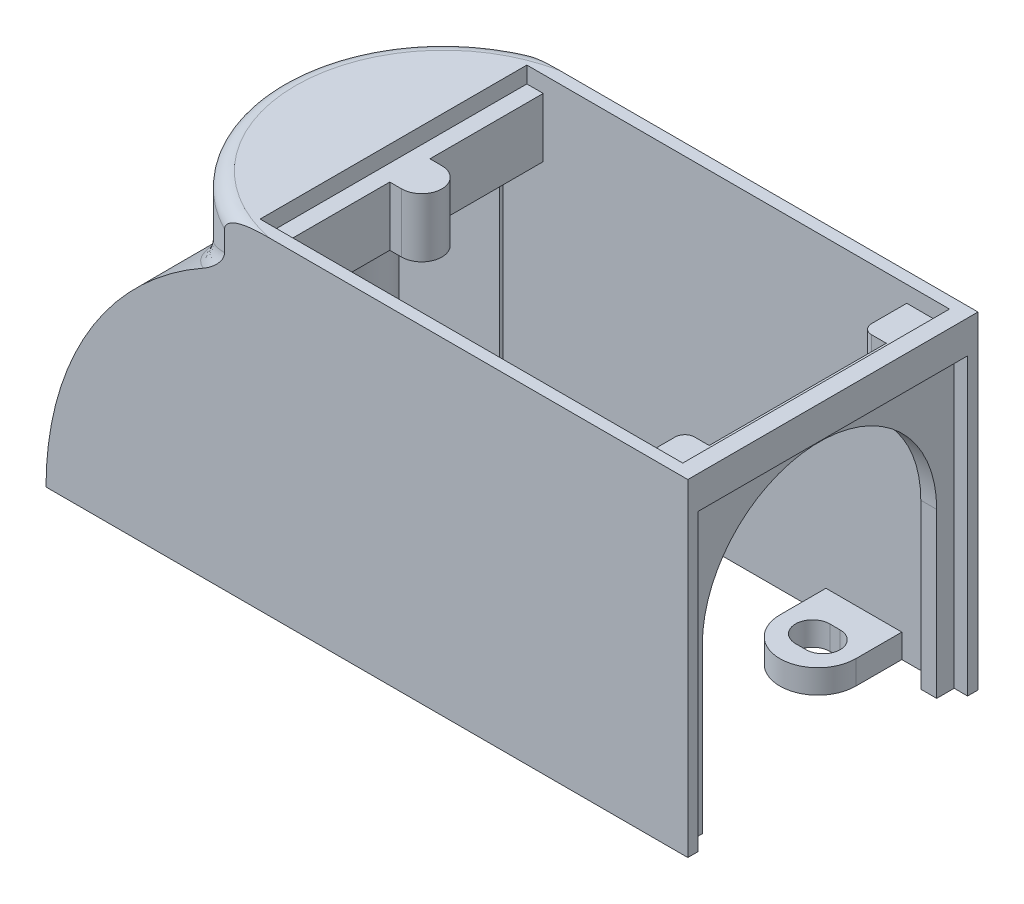
SolidWorks part; units mm, degrees
material "ABS"
ref_plane "Front Plane" through (0, 0, 0) normal (0, 0, 1) x (1, 0, 0)
ref_plane "Top Plane" through (0, 0, 0) normal (0, 1, 0) x (1, 0, 0)
ref_plane "Right Plane" through (0, 0, 0) normal (1, 0, 0) x (0, 0, -1)
sketch "Sketch1" plane through (0, 0, 0) normal (0, 1, 0) x (1, 0, 0)
  line L1 (0, 0) -> (75, 0)
  line L2 (0, 0) -> (0, 49.53)
  line L3 (0, 49.53) -> (75, 49.53)
  line L4 (75, 0) -> (75, 49.53)
  dimension "D1" = 49.53
  dimension "D2" = 75
extrude "Boss-Extrude1" add sketch "Sketch1" along normal blind 55.88
sketch "Sketch2" plane through (0, 55.88, 0) normal (0, 1, 0) x (1, 0, 0)
  line L0 (0, 0) -> (75, 0) construction
  line L1 (75, 49.53) -> (72, 49.53)
  line L2 (75, 49.53) -> (75, 0)
  line L3 (75, 0) -> (72, 0)
  line L4 (72, 49.53) -> (72, 0)
  line L5 (0, 49.53) -> (0, 0) construction
  line L6 (75, 49.53) -> (0, 49.53)
  line L7 (75, 49.53) -> (75, 47.53)
  line L8 (75, 47.53) -> (0, 47.53)
  line L9 (0, 49.53) -> (0, 47.53)
  line L10 (66.491, 41.529) -> (66.491, 49.53)
  line L11 (0, 49.53) -> (2.794, 49.53)
  line L12 (0, 49.53) -> (0, 0)
  line L13 (0, 0) -> (2.794, 0)
  line L14 (2.794, 49.53) -> (2.794, 0)
  line L15 (0, 0) -> (75, 0)
  line L16 (0, 0) -> (0, 2)
  line L17 (0, 2) -> (75, 2)
  line L18 (75, 0) -> (75, 2)
  line L19 (64.84, 41.529) -> (64.84, 47.53)
  line L20 (66.491, 39.878) -> (72, 39.878)
  line L21 (66.491, 0) -> (66.491, 8.001)
  line L22 (75, 8.001) -> (66.491, 8.001)
  line L23 (66.491, 9.652) -> (72, 9.652)
  line L24 (64.84, 8.001) -> (64.84, 2)
  line L25 (75, 24.765) -> (69, 24.765)
  line L26 (2.794, 24.765) -> (4.826, 24.765)
  line L27 (4.826, 28.194) -> (2.794, 28.194)
  line L28 (4.826, 21.336) -> (2.794, 21.336)
  line L29 (2.794, 49.53) -> (2.794, 47.53)
  line L30 (72, 49.53) -> (72, 47.53)
  line L31 (72, 0) -> (72, 2)
  line L32 (2.794, 0) -> (2.794, 2)
  line L33 (75, 41.529) -> (66.491, 41.529)
  line L34 (2.794, 2) -> (72, 2)
  line L35 (2.794, 2) -> (2.794, 47.53)
  line L36 (2.794, 47.53) -> (72, 47.53)
  line L37 (72, 2) -> (72, 47.53)
  line L38 (69, 24.765) -> (69, 47.53)
  line L39 (69, 47.53) -> (69, 2)
  circle A3 centre (4.826, 24.765) radius 3.429
  circle A4 centre (66.491, 41.529) radius 1.651
  circle A5 centre (66.491, 8.001) radius 1.651
  dimension "D7" = 6
  dimension "D8" = 6.858
  dimension "D11" = 3.302
  dimension "D1" = 3
  dimension "D2" = 2
  dimension "D3" = 2.794
  dimension "D4" = 2
  dimension "D5" = 9.652
  dimension "D6" = 10.16
  dimension "D9" = 2.032
extrude "Cut-Extrude1" cut sketch "Sketch2" against normal blind 51.816
sketch "Sketch3" plane through (0, 0, 0) normal (0, -1, 0) x (1, 0, 0)
  line L0 (51.046, -39.673) -> (51.046, -47.53)
  line L1 (75, -49.53) -> (0, -49.53) construction
  line L2 (64, -39.673) -> (64, -47.53)
  line L3 (75, 0) -> (75, -49.53) construction
  line L4 (56.634, -39.673) -> (58.412, -39.673) construction
  line L5 (0, -2) -> (75, -2)
  line L8 (0, -47.53) -> (0, -0.762)
  line L9 (0, 0) -> (75, 0) construction
  line L11 (51.046, -10.173) -> (51.046, -2)
  line L12 (64, -10.173) -> (64, -2)
  line L13 (56.634, -10.173) -> (58.412, -10.173) construction
  line L14 (56.634, -7.252) -> (58.412, -7.252)
  line L15 (56.634, -13.094) -> (58.412, -13.094)
  line L19 (21.546, 0) -> (8.546, 0)
  line L20 (21.546, 0) -> (21.546, -49.53)
  line L21 (21.546, -49.53) -> (8.546, -49.53)
  line L22 (8.546, 0) -> (8.546, -49.53)
  line L23 (70, -48.006) -> (70, 0)
  line L28 (0, -49.53) -> (0, 0) construction
  line L29 (70, 0) -> (73, 0)
  line L30 (70, 0) -> (70, -2.54)
  line L31 (70, -2.54) -> (73, -2.54)
  line L32 (73, 0) -> (73, -2.54)
  line L33 (75, 0) -> (0, 0)
  line L34 (75, 0) -> (75, -2)
  line L35 (75, -2) -> (0, -2)
  line L36 (0, 0) -> (0, -2)
  line L38 (75, -49.53) -> (0, -49.53)
  line L39 (75, -49.53) -> (75, -47.53)
  line L40 (75, -47.53) -> (0, -47.53)
  line L41 (0, -49.53) -> (0, -47.53)
  line L46 (56.634, -36.752) -> (58.412, -36.752)
  line L47 (56.634, -42.594) -> (58.412, -42.594)
  line L48 (75, -2) -> (75, -1)
  circle A3 centre (57.523, -10.173) radius 6.477
  arc A4 (56.634, -7.252) -> (56.634, -13.094) centre (56.634, -10.173) ccw
  arc A5 (58.412, -13.094) -> (58.412, -7.252) centre (58.412, -10.173) ccw
  circle A6 centre (57.523, -39.673) radius 6.477
  arc A7 (56.634, -36.752) -> (56.634, -42.594) centre (56.634, -39.673) ccw
  arc A8 (58.412, -42.594) -> (58.412, -36.752) centre (58.412, -39.673) ccw
  point P29 (57.523, -10.173)
  point P34 (53.713, -10.173)
  point P35 (61.333, -10.173)
  point P69 (57.523, -39.673)
  point P75 (53.713, -39.673)
  point P76 (61.333, -39.673)
  dimension "D7" = 12.954
  dimension "D19" = 7.62
  dimension "D13" = 11
  dimension "D2" = 5
  dimension "D3" = 2
  dimension "D4" = 11
  dimension "D5" = 29.5
  dimension "D6" = 10.173
  dimension "D8" = 5.842
  dimension "D9" = 7.62
  dimension "D10" = 13
  dimension "D11" = 2
  dimension "D12" = 29.5
  dimension "D15" = 2.54
  dimension "D16" = 2
  dimension "D18" = 5.842
extrude "Cut-Extrude2" cut sketch "Sketch3" against normal blind 43
sketch "Sketch5" plane through (75, 0, 0) normal (1, 0, 0) x (0, 0, -1)
  line L0 (0, 0) -> (1.5875, 0)
  line L1 (0, 0) -> (49.53, 0) construction
  line L2 (0, 0) -> (4.7625, 0)
  line L3 (1.5875, 0) -> (1.524, 55.88)
  line L4 (4.7625, 0) -> (4.7625, 55.88)
  line L5 (0, 55.88) -> (49.53, 55.88) construction
  line L6 (49.53, 0) -> (47.9425, 0)
  line L7 (49.53, 0) -> (44.7675, 0)
  line L8 (44.7675, 0) -> (44.7675, 55.88)
  line L9 (47.9425, 0) -> (47.9425, 55.88)
  line L10 (24.765, 55.88) -> (24.765, 51.1175)
  line L11 (24.765, 55.88) -> (24.765, 47.9425)
  line L12 (4.7625, 47.9425) -> (44.7675, 47.9425)
  line L13 (4.7625, 0) -> (44.7675, 0)
  line L14 (4.7625, 0) -> (4.7625, 4.318)
  line L15 (4.7625, 4.318) -> (44.7675, 4.318)
  line L16 (44.7675, 0) -> (44.7675, 4.318)
  circle A0 centre (24.765, 27.94) radius 20.0025
  dimension "D1" = 4.7625
  dimension "D2" = 1.5875
  dimension "D3" = 4.7625
  dimension "D4" = 7.9375
  dimension "D5" = 4.318
extrude "Cut-Extrude3" cut sketch "Sketch5" along direction (-1, 0, 0) on the side against the normal up to surface (53.454 mm away) contours A0 L4 L15 L8 | A0
sketch "Sketch8" plane through (0, 55.88, 0) normal (0, 1, 0) x (1, 0, 0)
  line L0 (75, 24.765) -> (72.206, 24.765)
  line L1 (75, 0) -> (75, 49.53) construction
  line L2 (0, 0) -> (75, 0) construction
  line L3 (75, 49.53) -> (72.136, 49.53)
  line L4 (75, 49.53) -> (75, 0)
  line L5 (75, 0) -> (72.136, 0)
  line L6 (72.136, 49.53) -> (72.136, 0)
  line L7 (64.84, 47.53) -> (72.136, 47.53)
  line L8 (64.84, 47.53) -> (64.84, 41.529)
  line L9 (66.491, 39.878) -> (69, 39.878)
  line L10 (69, 39.878) -> (69, 9.652)
  line L11 (69, 9.652) -> (66.491, 9.652)
  line L12 (64.84, 8.001) -> (64.84, 2)
  line L13 (64.84, 2) -> (72.136, 2)
  circle A0 centre (66.421, 41.529) radius 1.651
  circle A1 centre (66.491, 8.001) radius 1.651
  arc M6 (66.491, 9.652) -> (64.84, 8.001) centre (66.491, 8.001) ccw
  line M7 (64.84, 8.001) -> (64.84, 2)
  line M15 (64.84, 47.53) -> (64.84, 41.529)
  arc M16 (64.84, 41.529) -> (66.491, 39.878) centre (66.491, 41.529) ccw
  line M17 (66.491, 39.878) -> (69, 39.878)
  line M18 (69, 39.878) -> (69, 9.652)
  line M19 (69, 9.652) -> (66.491, 9.652)
  dimension "D1" = 2.794
extrude "Cut-Extrude4" cut sketch "Sketch8" against normal blind 2.794 contours A1 L13 L6 L7 A0 M7 M15 M17 M18 M19 | A0 M16 | A1 M6
sketch "Sketch9" plane through (0, 4.318, 0) normal (0, 1, 0) x (1, 0, 0)
  line L0 (70, 44.7675) -> (75, 44.7675)
  line L1 (75, 44.7675) -> (75, 4.7625)
  line L2 (75, 4.7625) -> (70, 4.7625)
  line L3 (70, 4.7625) -> (70, 44.7675)
  line L4 (70, 4.7625) -> (70, 44.7675) construction
extrude "Cut-Extrude5" cut sketch "Sketch9" against normal up to next
sketch "Sketch10" plane through (75, 0, 0) normal (1, 0, 0) x (0, 0, -1)
  line L0 (0, 0) -> (1.778, 0)
  line L1 (2, 0) -> (47.53, 0) construction
  line L2 (49.53, 0) -> (47.752, 0)
  line L3 (1.778, 0) -> (47.752, 0)
  line L4 (1.778, 0) -> (1.778, 50.292)
  line L5 (1.778, 50.292) -> (47.752, 50.292)
  line L6 (47.752, 0) -> (47.752, 50.292)
  line M7 (44.7675, 27.94) -> (44.7675, 0)
  line M8 (44.7675, 0) -> (49.53, 0)
  line M12 (0, 0) -> (4.7625, 0)
  line M13 (4.7625, 0) -> (4.7625, 27.94)
  arc M14 (4.7625, 27.94) -> (44.7675, 27.94) centre (24.765, 27.94) cw
  dimension "D1" = 1.778
  dimension "D2" = 50.292
extrude "Cut-Extrude6" cut sketch "Sketch10" against normal blind 2.286 contours L6 L5 L4 M8 M12 M13 M14 M7
sketch "Sketch11" plane through (0, 55.88, 0) normal (0, 1, 0) x (1, 0, 0)
  line L0 (2.794, 49.53) -> (2.794, 28.194)
  line L1 (75, 49.53) -> (0, 49.53) construction
  line L2 (2.794, 49.53) -> (0, 49.53)
  line L3 (0, 49.53) -> (0, 0)
  line L4 (0, 0) -> (2.794, 0)
  line L5 (0, 0) -> (75, 0) construction
  line L6 (2.794, 0) -> (2.794, 21.336)
  line L7 (2.794, 21.336) -> (4.826, 21.336)
  line L8 (2.794, 28.194) -> (4.826, 28.194)
  line L9 (2.794, 47.53) -> (0, 47.53)
  line L10 (2.794, 2) -> (0, 2)
  circle A0 centre (4.826, 24.765) radius 3.5
  line M1 (0, 49.53) -> (0, 0)
  line M2 (0, 0) -> (75, 0)
  line M4 (75, 49.53) -> (0, 49.53)
  line M8 (2.794, 2) -> (2.794, 21.336)
  line M9 (2.794, 21.336) -> (4.826, 21.336)
  arc M10 (4.826, 21.336) -> (4.826, 28.194) centre (4.826, 24.765) ccw
  line M11 (4.826, 28.194) -> (2.794, 28.194)
  line M12 (2.794, 28.194) -> (2.794, 47.53)
  dimension "D1" = 7
extrude "Cut-Extrude7" cut sketch "Sketch11" against normal blind 2.794 contours A0 L0 L6 M11 M12 M4 M1 M2 M8 M9 | A0 M10
sketch "Sketch12" plane through (0, 0, 0) normal (-1, 0, 0) x (0, 0, 1)
  line L1 (-49.53, 55.88) -> (-49.53, 0)
  line L2 (-49.53, 0) -> (-47.53, 0)
  line L3 (-47.53, 0) -> (-47.53, 43)
  line L4 (-47.53, 43) -> (-2, 43)
  line L5 (-2, 43) -> (-2, 0)
  line L6 (-2, 0) -> (0, 0)
  line L7 (0, 0) -> (0, 55.88)
  line L12 (-49.53, 55.88) -> (0, 55.88)
extrude "Boss-Extrude2" add sketch "Sketch12" along normal blind 4.064
sketch "Sketch13" plane through (0, 0, 0) normal (0, 0, 1) x (1, 0, 0)
  line L0 (-4.064, 47.625) -> (-4.064, 0) construction
  line L1 (-4.064, 0) -> (-34.544, 0)
  line L4 (-4.064, 0) -> (75, 0) construction
  arc A0 (-4.064, 47.625) -> (-34.544, 0) centre (17.903, 0) ccw
  dimension "D3" = 30.48
  dimension "D4" = 47.625
extrude "Boss-Extrude3" add sketch "Sketch13" against normal up to surface (49.53 mm away) up to face at (35.468, 27.94, -49.53)
sketch "Sketch14" plane through (0, 0, 0) normal (0, 0, 1) x (1, 0, 0)
  line L0 (-34.544, 0) -> (75, 0) construction
  line L2 (-34.544, 0) -> (75, 0)
  line L4 (-4.064, 55.88) -> (-4.064, 0)
  circle A1 centre (17.903, 0) radius 50.447
  arc A2 (-4.064, 47.625) -> (-34.544, 0) centre (17.903, 0) ccw construction
  arc A3 (-4.064, 47.625) -> (-34.544, 0) centre (17.903, 0) ccw
  dimension "D1" = 2
extrude "Cut-Extrude8" cut sketch "Sketch14" along direction (0, 0, 1) on the side against the normal up to surface (49.53 mm away)
sketch "Sketch15" plane through (0, 0, 0) normal (0, 0, 1) x (1, 0, 0)
  line L0 (-34.544, 0) -> (-4.064, 0)
  line L1 (-4.064, 0) -> (-4.064, 47.625)
  arc A1 (-4.064, 45.4131) -> (-32.544, 0) centre (17.903, 0) ccw construction
  arc A2 (-4.064, 45.4131) -> (-32.544, 0) centre (17.903, 0) ccw
extrude "Boss-Extrude4" add sketch "Sketch15" against normal blind 2.6
sketch "Sketch16" plane through (0, 0, -49.53) normal (0, 0, -1) x (-1, 0, 0)
  line L0 (4.064, 47.625) -> (4.064, 0)
  line L1 (4.064, 0) -> (46.99, 0)
extrude "Boss-Extrude5" add sketch "Sketch16" against normal blind 2.6
sketch "Sketch18" plane through (0, 55.88, 0) normal (0, 1, 0) x (1, 0, 0)
  line L0 (8.546, 47.53) -> (8.546, 2) construction
  line L1 (-4.064, 49.53) -> (-4.064, 0)
  circle A0 centre (8.546, 24.765) radius 27.7906
  line M6 (-4.064, 49.53) -> (-4.064, 0)
extrude "Boss-Extrude6" add sketch "Sketch18" against normal up to surface (8.255 mm away) contours A0 M6
sketch "Sketch19" plane through (0, 0, 0) normal (0, -1, 0) x (1, 0, 0)
  line L0 (-25.283, -33.53) -> (-34.544, -33.53)
  line L1 (-34.544, 0) -> (75, 0) construction
  line L2 (-18.044, -40.769) -> (-18.044, -49.53)
  line L3 (-25.283, -16) -> (-34.544, -16)
  line L5 (-18.044, -8.761) -> (-18.044, 0)
  line L6 (75, -49.53) -> (-34.544, -49.53) construction
  line L7 (-26.172, -8.761) -> (-24.394, -8.761) construction
  line L8 (-26.172, -5.84) -> (-24.394, -5.84)
  line L9 (-26.172, -11.682) -> (-24.394, -11.682)
  line L10 (-26.172, -40.769) -> (-24.394, -40.769) construction
  line L11 (-26.172, -37.848) -> (-24.394, -37.848)
  line L12 (-26.172, -43.69) -> (-24.394, -43.69)
  line L13 (-34.544, -49.53) -> (-34.544, 0) construction
  circle A0 centre (-25.283, -8.761) radius 7.239
  circle A1 centre (-25.283, -40.769) radius 7.239
  arc A2 (-26.172, -5.84) -> (-26.172, -11.682) centre (-26.172, -8.761) ccw
  arc A3 (-24.394, -11.682) -> (-24.394, -5.84) centre (-24.394, -8.761) ccw
  arc A4 (-26.172, -37.848) -> (-26.172, -43.69) centre (-26.172, -40.769) ccw
  arc A5 (-24.394, -43.69) -> (-24.394, -37.848) centre (-24.394, -40.769) ccw
  point P21 (-25.283, -8.761)
  point P26 (-29.093, -8.761)
  point P27 (-21.473, -8.761)
  point P30 (-25.283, -40.769)
  point P35 (-29.093, -40.769)
  point P36 (-21.473, -40.769)
  line M19 (-4.064, -46.93) -> (-32.544, -46.93)
  line M20 (-32.544, -46.93) -> (-32.544, -2.6)
  line M21 (-32.544, -2.6) -> (-4.064, -2.6)
  dimension "D3" = 14.478
  dimension "D1" = 16
  dimension "D2" = 16.5
  dimension "D4" = 5.842
  dimension "D5" = 7.62
  dimension "D6" = 5.842
  dimension "D7" = 7.62
  dimension "D8" = 32.008
extrude "Boss-Extrude7" add sketch "Sketch19" against normal up to surface (18.3617 mm away) contours A0 A3 L9 A2 L8 M21 M20 | A1 A5 L12 A4 L11 M19 M20
sketch "Sketch20" plane through (0, 0, 0) normal (0, -1, 0) x (1, 0, 0)
  line L0 (-26.172, -40.769) -> (-24.394, -40.769) construction
  line L1 (-26.172, -37.848) -> (-24.394, -37.848)
  line L2 (-26.172, -43.69) -> (-24.394, -43.69)
  line L3 (-26.172, -8.761) -> (-24.394, -8.761) construction
  line L4 (-26.172, -5.84) -> (-24.394, -5.84)
  line L5 (-26.172, -11.682) -> (-24.394, -11.682)
  circle A0 centre (-25.283, -8.761) radius 7.239
  circle A1 centre (-25.283, -40.769) radius 7.239
  arc A2 (-26.172, -37.848) -> (-26.172, -43.69) centre (-26.172, -40.769) ccw
  arc A3 (-24.394, -43.69) -> (-24.394, -37.848) centre (-24.394, -40.769) ccw
  arc A4 (-26.172, -5.84) -> (-26.172, -11.682) centre (-26.172, -8.761) ccw
  arc A5 (-24.394, -11.682) -> (-24.394, -5.84) centre (-24.394, -8.761) ccw
  circle A6 centre (-25.283, -8.761) radius 6.096
  circle A7 centre (-25.283, -40.769) radius 6.096
  point P8 (-25.283, -40.769)
  point P13 (-29.093, -40.769)
  point P14 (-21.473, -40.769)
  point P17 (-25.283, -8.761)
  point P22 (-29.093, -8.761)
  point P23 (-21.473, -8.761)
  dimension "D5" = 12.192
  dimension "D6" = 12.192
  dimension "D1" = 5.842
  dimension "D2" = 7.62
  dimension "D3" = 5.842
  dimension "D4" = 7.62
extrude "Cut-Extrude9" cut sketch "Sketch20" against normal through all from offset 4.318 contours A6 A5 L5 A4 L4 | L5 A5 L4 A4 | L2 A3 L1 A2 | A7 A3 L2 A2 L1 offset against normal yes
fillet "Fillet1" radius 2.54 2 edges at (-19.0882, 37.1798, -21.8212) (-19.2446, 55.88, -24.765)
